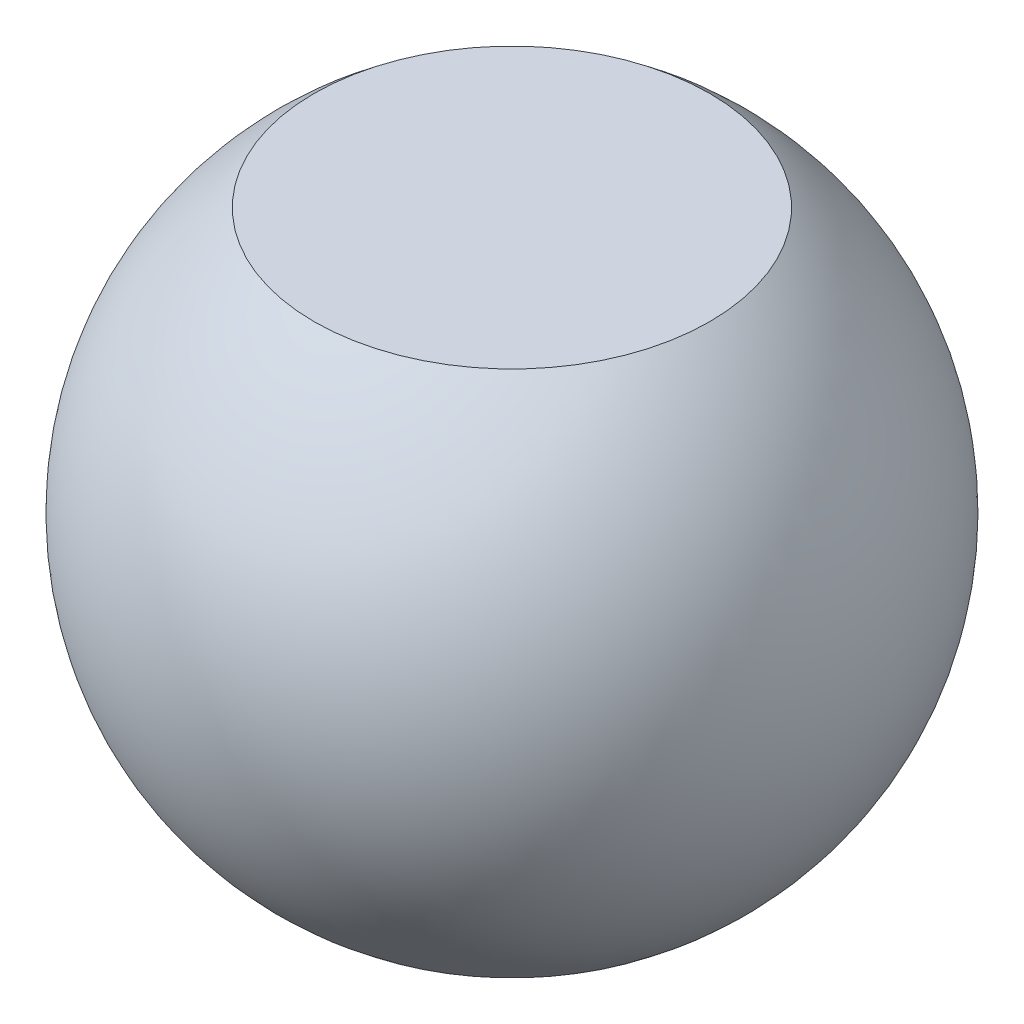
SolidWorks part; units mm, degrees
ref_plane "Front Plane" through (0, 0, 0) normal (0, 0, 1) x (1, 0, 0)
ref_plane "Top Plane" through (0, 0, 0) normal (0, 1, 0) x (1, 0, 0)
ref_plane "Right Plane" through (0, 0, 0) normal (1, 0, 0) x (0, 0, -1)
sketch "Sketch1" plane through (0, 0, 0) normal (0, 0, 1) x (1, 0, 0)
  line L0 (0, 0.3) -> (0, -0.3)
  line L1 (0, 0.3) -> (0.225, 0.3)
  line L2 (0, -0.3) -> (0.225, -0.3)
  arc A0 (0.225, -0.3) -> (0.225, 0.3) centre (0, 0) ccw
  dimension "D1" = 0.75
  dimension "D2" = 0.3
  dimension "D3" = 0.3
revolve "Revolve1" add sketch "Sketch1" angle 360 about L0
